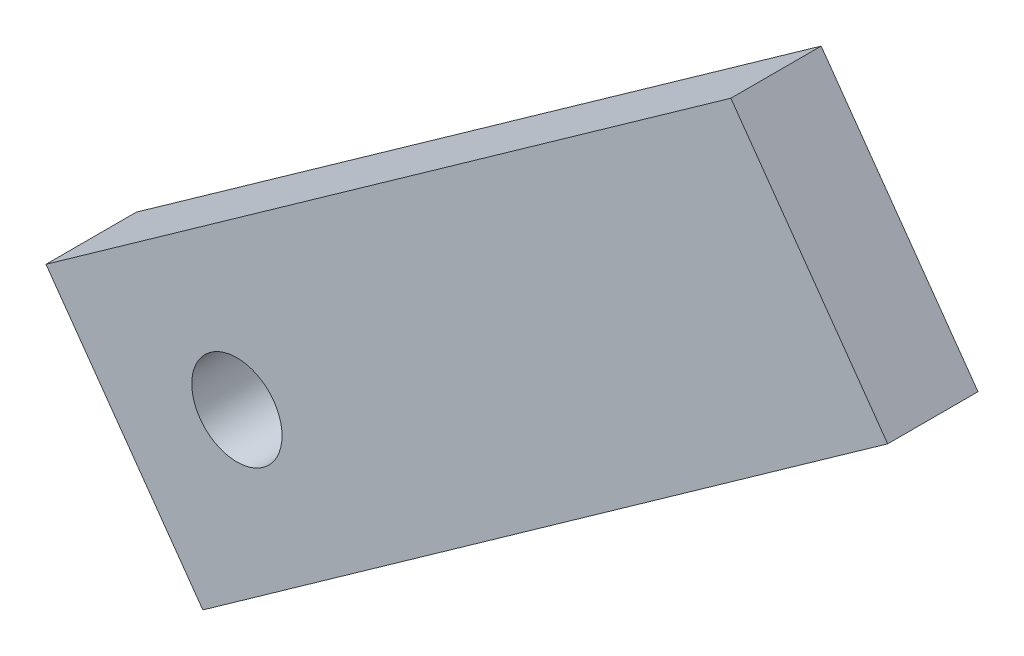
SolidWorks part; units mm, degrees
ref_plane "Front Plane" through (0, 0, 0) normal (0, 0, 1) x (1, 0, 0)
ref_plane "Top Plane" through (0, 0, 0) normal (0, 1, 0) x (1, 0, 0)
ref_plane "Right Plane" through (0, 0, 0) normal (1, 0, 0) x (0, 0, -1)
sketch "Sketch1" plane through (0, 0, 0) normal (0, 0, 1) x (1, 0, 0)
  line L0 (-67.8067, 8.4523) -> (-48.5457, 22.1276)
  line L1 (-67.8067, 8.4523) -> (-63.3953, 2.2391)
  line L2 (-63.3953, 2.2391) -> (-44.1343, 15.9144)
  line L3 (-44.1343, 15.9144) -> (-48.5457, 22.1276)
  line L5 (-64.6431, 10.6985) -> (-60.2317, 4.4852)
  line L6 (-65.601, 5.3457) -> (-46.34, 19.021)
  circle A0 centre (-62.4374, 7.5919) radius 1.27
  dimension "D1" = 23.622
extrude "Boss-Extrude2" add sketch "Sketch1" along normal blind 2.54 contours A0 L6 L3 L0 L5 | A0 L5 L2 L3 L6 | A0 L6 L1 L2 L5 | A0 L5 L0 L1 L6
